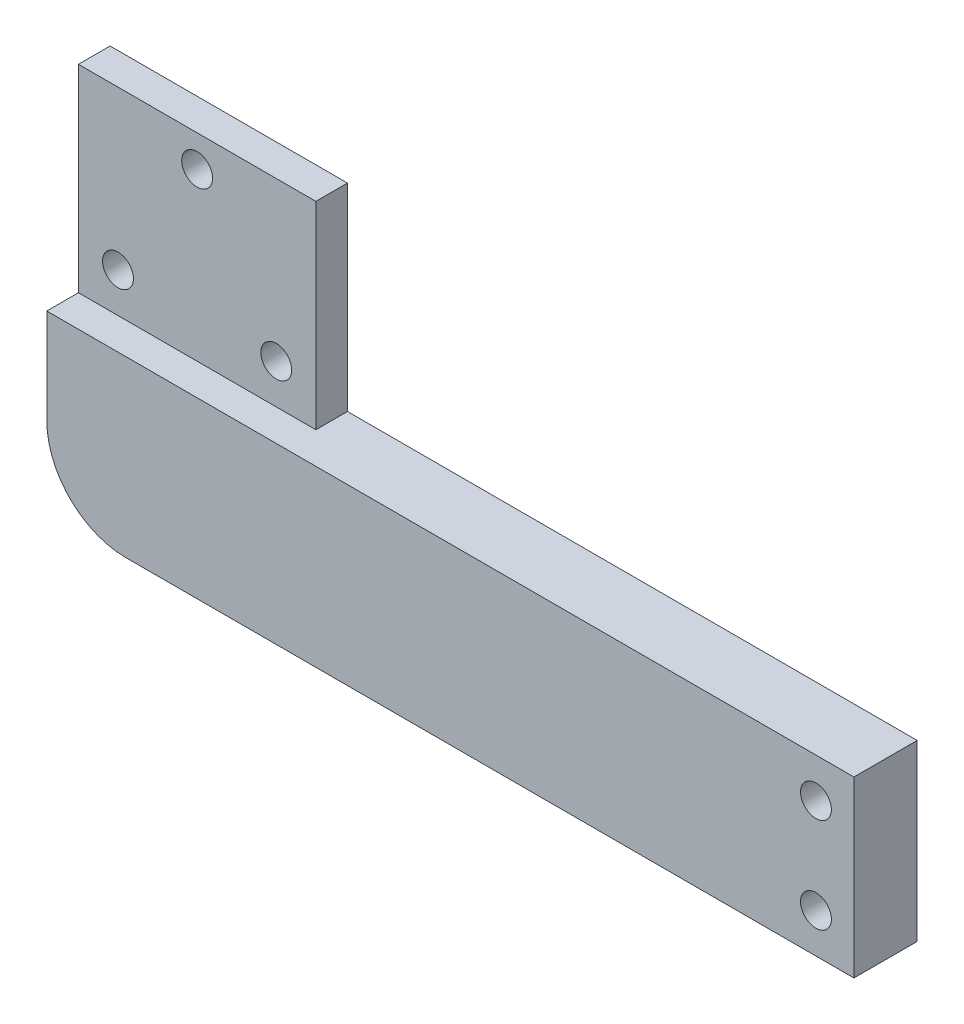
SolidWorks part; units mm, degrees
material "PLA Black"
ref_plane "Front Plane" through (0, 0, 0) normal (0, 0, 1) x (1, 0, 0)
ref_plane "Top Plane" through (0, 0, 0) normal (0, 1, 0) x (1, 0, 0)
ref_plane "Right Plane" through (0, 0, 0) normal (1, 0, 0) x (0, 0, -1)
sketch "Sketch1" plane through (0, 0, 0) normal (0, 0, 1) x (1, 0, 0)
  line L1 (51, 11) -> (-51, 11)
  line L2 (51, 11) -> (51, -11)
  line L3 (51, -11) -> (-51, -11)
  line L4 (-51, 11) -> (-51, -11)
  point P4 (51, 0)
  point P6 (0, 11)
  dimension "D1" = 102
  dimension "D2" = 22
extrude "Extrude1" add sketch "Sketch1" along normal blind 8
hole_wizard "Ø4.0 (4) Diameter Hole1" positions "3DSketch1" profile "Sketch2" hole size "Ø4.0" standard "Ansi Metric"
sketch3d "3DSketch1"
  line L0 (51, -11, 8) -> (51, 11, 8) construction
  line L1 (51, 11, 8) -> (-51, 11, 8) construction
  point P0 (46.2, 6, 8)
  point P2 (46.2, -6, 8)
  dimension "D1" = 4.8
  dimension "D2" = 12
  dimension "D3" = 5
sketch "Sketch2" plane through (46.2, 6, 8) normal (1, 0, 0) x (0, -1, 0)
  line L0 (0, 0) -> (0, 15)
  line L1 (0, 15) -> (1.95, 15)
  line L2 (1.95, 15) -> (1.95, 0)
  line L5 (1.95, 0) -> (0, 0)
  line L10 (0, 15) -> (-1.95, 15) construction
  line L11 (0, -6.35) -> (0, 107.95) construction
  dimension "Hole Dia." = 3.9
  dimension "Hole Depth" = 15
  dimension "Drill Angle" = 180
sketch "Sketch3" plane through (0, 0, 0) normal (0, 0, 1) x (1, 0, 0)
  line L1 (-51, 11) -> (-21, 11)
  line L2 (-51, 11) -> (-51, 36)
  line L3 (-51, 36) -> (-21, 36)
  line L4 (-21, 11) -> (-21, 36)
  dimension "D1" = 25
  dimension "D2" = 30
extrude "Extrude2" add sketch "Sketch3" along normal blind 8
fillet "Fillet1" radius 10 1 edges at (-51, -11, 4)
hole_wizard "Ø4.0 (4) Diameter Hole2" positions "3DSketch2" profile "Sketch4" hole size "Ø4.0" standard "Ansi Metric"
sketch3d "3DSketch2"
  line L0 (-36, 36, 8) -> (-36, -0.4475, 8) construction
  line L1 (-21, 36, 8) -> (-51, 36, 8) construction
  line L2 (-46, 16, 8) -> (-26, 16, 8) construction
  point P0 (-46, 16, 8)
  point P2 (-26, 16, 8)
  point P4 (-36, 32, 8)
  point P16 (-36, 16, 8)
  dimension "D1" = 4
  dimension "D2" = 20
  dimension "D3" = 16
sketch "Sketch4" plane through (-46, 16, 8) normal (1, 0, 0) x (0, -1, 0)
  line L0 (0, 0) -> (0, 15)
  line L1 (0, 15) -> (1.95, 15)
  line L2 (1.95, 15) -> (1.95, 0)
  line L5 (1.95, 0) -> (0, 0)
  line L10 (0, 15) -> (-1.95, 15) construction
  line L11 (0, -6.35) -> (0, 107.95) construction
  dimension "Hole Dia." = 3.9
  dimension "Hole Depth" = 15
  dimension "Drill Angle" = 180
sketch "Sketch5" plane through (0, 0, 8) normal (0, 0, 1) x (1, 0, 0)
  line L0 (-51, 36) -> (-51, -1) construction
  line L1 (-21, 36) -> (-51, 36)
  line L2 (-21, 36) -> (-21, 11)
  line L3 (-21, 11) -> (-51, 11)
  line L4 (-51, 36) -> (-51, 11)
  dimension "D1" = 25
extrude "Extrude3" cut sketch "Sketch5" against normal blind 4
